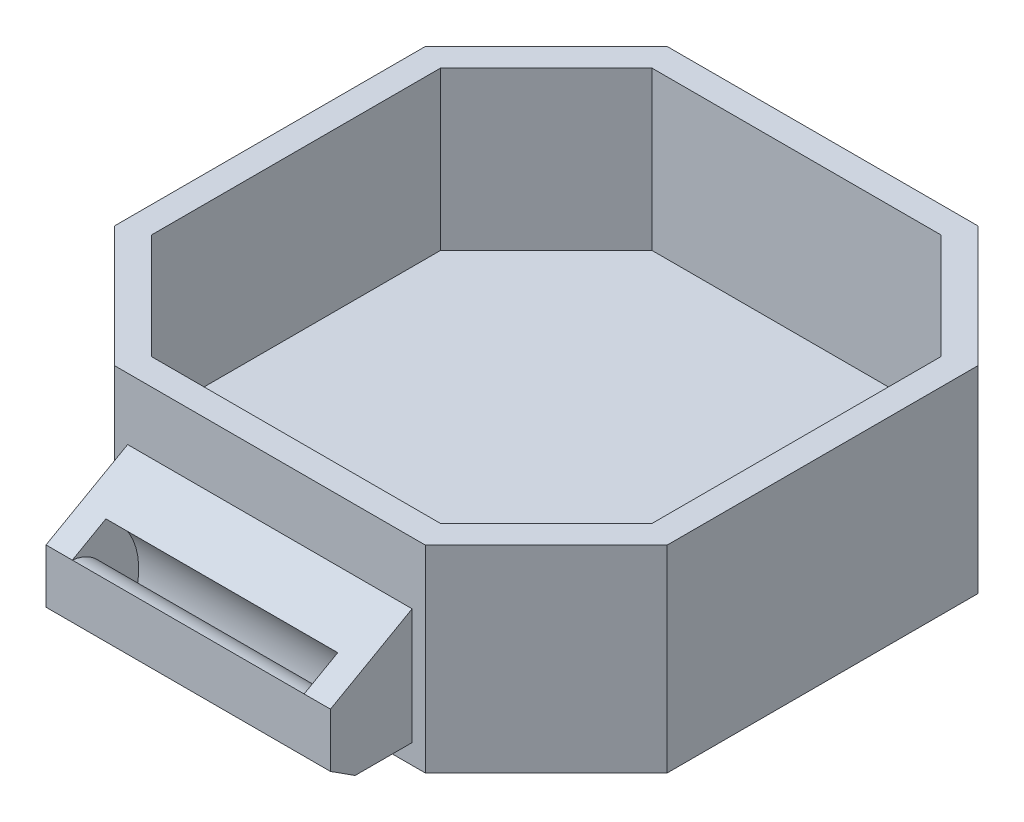
SolidWorks part; units mm, degrees
ref_plane "Front Plane" through (0, 0, 0) normal (0, 0, 1) x (1, 0, 0)
ref_plane "Top Plane" through (0, 0, 0) normal (0, 1, 0) x (1, 0, 0)
ref_plane "Right Plane" through (0, 0, 0) normal (1, 0, 0) x (0, 0, -1)
sketch "Sketch2" plane through (0, 0, 0) normal (0, 1, 0) x (1, 0, 0)
  line L0 (-21, 11.8076) -> (-21, -11.8076)
  line L1 (-21, -11.8076) -> (-11.8076, -21)
  line L2 (-11.8076, -21) -> (11.8076, -21)
  line L3 (11.8076, -21) -> (21, -11.8076)
  line L4 (21, -11.8076) -> (21, 11.8076)
  line L5 (21, 11.8076) -> (11.8076, 21)
  line L6 (11.8076, 21) -> (-11.8076, 21)
  line L7 (-11.8076, 21) -> (-21, 11.8076)
  point P2 (-21, 0)
  point P9 (14.1114, -11.6843)
  point P11 (21, 0)
  point P12 (0, 21)
  point P13 (21, -11.0123)
  point P14 (21, -12.4105)
  dimension "D1" = 42
  dimension "D2" = 13
extrude "Boss-Extrude1" add sketch "Sketch2" along normal blind 15 contours L7 L0 L1 L2 L3 L4 L5 L6
sketch "Sketch3" plane through (0, 15, 0) normal (0, 1, 0) x (1, 0, 0)
  line L16 (10.9792, 19) -> (-10.9792, 19)
  line L17 (-10.9792, 19) -> (-19, 10.9792)
  line L18 (-19, 10.9792) -> (-19, -10.9792)
  line L19 (-19, -10.9792) -> (-10.9792, -19)
  line L20 (-10.9792, -19) -> (10.9792, -19)
  line L21 (10.9792, -19) -> (19, -10.9792)
  line L22 (19, -10.9792) -> (19, 10.9792)
  line L23 (19, 10.9792) -> (10.9792, 19)
  line L24 (10.9792, 19) -> (-10.9792, 19)
  line L25 (-10.9792, 19) -> (-19, 10.9792)
  line L26 (-19, 10.9792) -> (-19, -10.9792)
  line L27 (-19, -10.9792) -> (-10.9792, -19)
  line L28 (-10.9792, -19) -> (10.9792, -19)
  line L29 (10.9792, -19) -> (19, -10.9792)
  line L30 (19, -10.9792) -> (19, 10.9792)
  line L31 (19, 10.9792) -> (10.9792, 19)
  dimension "D1" = 2
extrude "Cut-Extrude1" cut sketch "Sketch3" against normal blind 12 contours L26 L27 L28 L29 L30 L31 L24 L25
sketch "Sketch4" plane through (0, 0, 21) normal (0, 0, 1) x (1, 0, 0)
  line L0 (-11.8076, 0) -> (11.8076, 0) construction
  line L1 (-10.8076, 1.5) -> (10.8076, 1.5)
  line L2 (-10.8076, 1.5) -> (-10.8076, 12)
  line L3 (-10.8076, 12) -> (10.8076, 12)
  line L4 (10.8076, 1.5) -> (10.8076, 12)
  line L5 (-11.8076, 15) -> (11.8076, 15) construction
  line L6 (11.8076, 15) -> (11.8076, 0) construction
  line L8 (-11.8076, 15) -> (-11.8076, 0) construction
  dimension "D1" = 1
  dimension "D2" = 1.5
  dimension "D3" = 3
  dimension "D4" = 1
extrude "Boss-Extrude2" add sketch "Sketch4" along normal blind 12
sketch "Sketch5" plane through (10.8076, 0, 0) normal (1, 0, 0) x (0, 0, -1)
  line L0 (-25.3317, 1.5) -> (-27.2042, 2.7026)
  line L1 (-33, 1.5) -> (-21, 1.5) construction
  line L2 (-27.2042, 2.7026) -> (-27.2042, 6.8027)
  line L3 (-27.2042, 6.8027) -> (-21, 10.3041)
  line L4 (-21, 1.5) -> (-21, 12) construction
  line L7 (-33, 1.5) -> (-33, 12) construction
  line L8 (-33, 12) -> (-21, 12) construction
  line L9 (-33, 1.5) -> (-25.3317, 1.5)
  line L10 (-33, 1.5) -> (-33, 12)
  line L11 (-33, 12) -> (-21, 12)
  line L12 (-21, 12) -> (-21, 10.3041)
extrude "Cut-Extrude2" cut sketch "Sketch5" against normal through all
ref_plane "Plane1" through (8.8076, 0, 0) normal (1, 0, 0) x (0, 0, -1)
ref_plane "Plane2" through (-8.8076, 0, 0) normal (-1, 0, 0) x (0, 0, 1)
sketch "Sketch6" plane through (8.8076, 0, 0) normal (1, 0, 0) x (0, 0, -1)
  line L2 (-25.3317, 1.5) -> (-27.2042, 2.7026) construction
  line L4 (-27.2042, 6.8027) -> (-21, 10.3041) construction
  line L6 (-27.2042, 6.8027) -> (-24.6522, 8.243)
  line L7 (-25.3317, 1.5) -> (-21, 1.5) construction
  line L8 (-25.3317, 1.5) -> (-22.6306, 1.5)
  arc A0 (-27.2042, 6.8027) -> (-25.3317, 1.5) centre (-27.5316, 3.7052) cw
  arc A1 (-24.6522, 8.243) -> (-22.6306, 1.5) centre (-27.5316, 3.7052) cw
extrude "Cut-Extrude4" cut sketch "Sketch6" against normal up to surface (17.6152 mm away)
